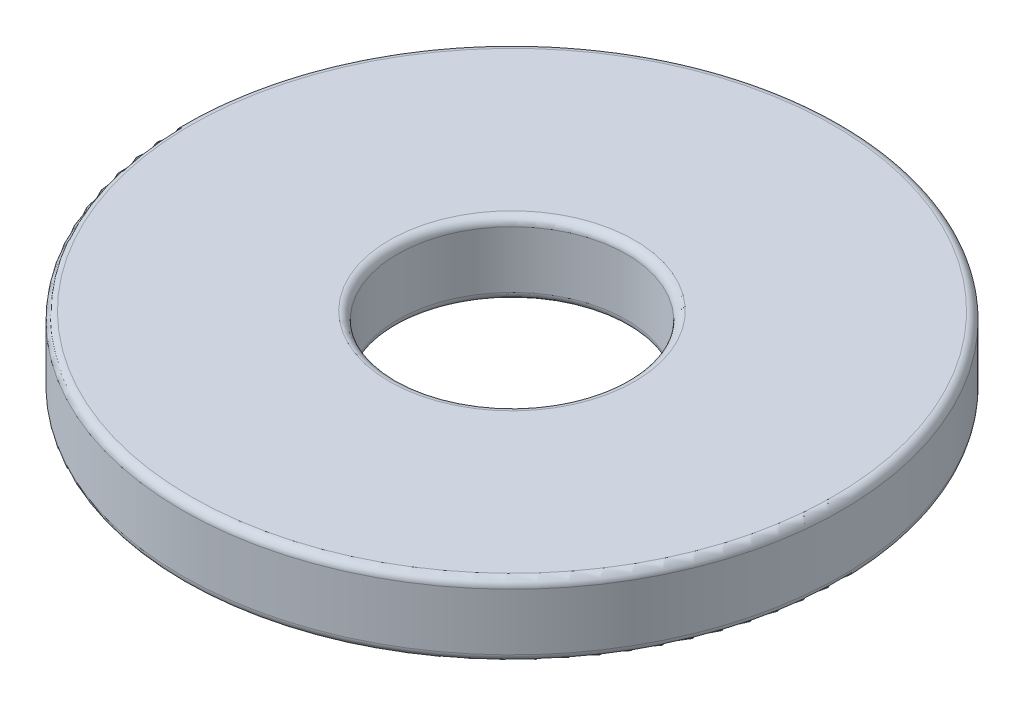
SolidWorks part; units mm, degrees
material "AISI 347 Annealed Stainless Steel (SS)"
ref_plane "Front Plane" through (0, 0, 0) normal (0, 0, 1) x (1, 0, 0)
ref_plane "Top Plane" through (0, 0, 0) normal (0, 1, 0) x (1, 0, 0)
ref_plane "Right Plane" through (0, 0, 0) normal (1, 0, 0) x (0, 0, -1)
sketch "Sketch1" plane through (0, 0, 0) normal (0, 1, 0) x (1, 0, 0)
  circle A0 centre (0, 0) radius 5.1562
  circle A1 centre (0, 0) radius 1.7907
  dimension "D1" = 10.3124
  dimension "D2" = 3.5814
extrude "Boss-Extrude1" add sketch "Sketch1" along normal blind 1.143
fillet "Fillet1" radius 0.127 1 edges at (0, 1.143, 5.1562)
fillet "Fillet2" radius 0.127 1 edges at (0, 0, 5.1562)
fillet "Fillet3" radius 0.127 2 edges at (0, 1.143, 1.7907) (0, 0, 1.7907)
